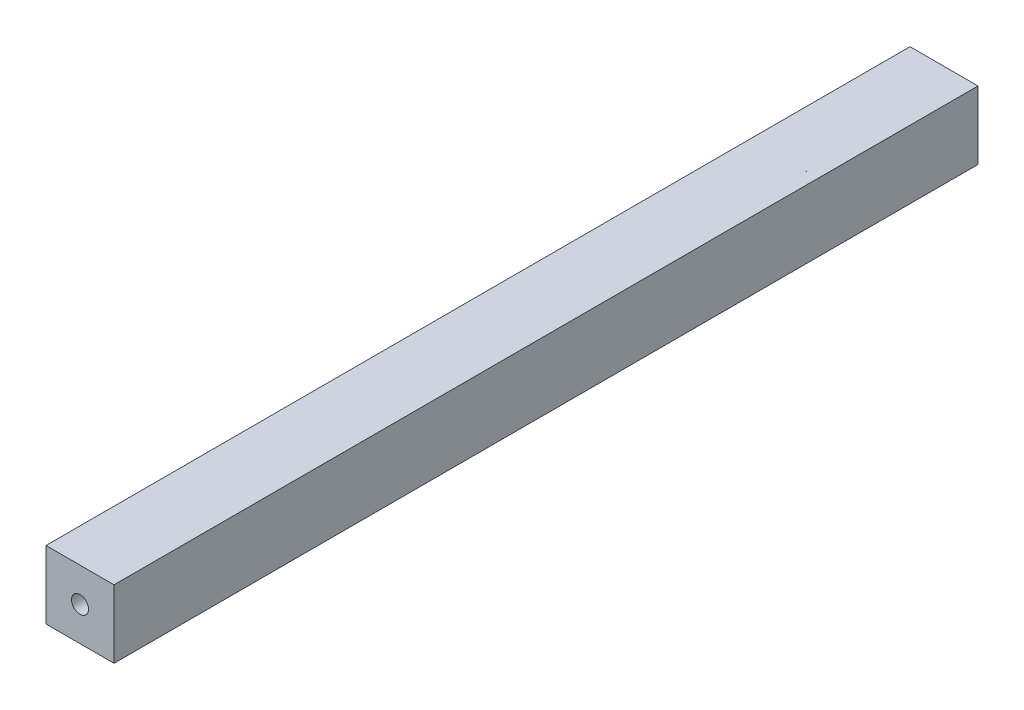
SolidWorks part; units mm, degrees
ref_plane "Front" through (0, 0, 0) normal (0, 0, 1) x (1, 0, 0)
ref_plane "Top" through (0, 0, 0) normal (0, 1, 0) x (1, 0, 0)
ref_plane "Right" through (0, 0, 0) normal (1, 0, 0) x (0, 0, -1)
sketch "Sketch1" plane through (0, 0, 0) normal (0, 0, 1) x (1, 0, 0)
  line L1 (10, 10) -> (-10, 10)
  line L2 (10, 10) -> (10, -10)
  line L3 (10, -10) -> (-10, -10)
  line L4 (-10, 10) -> (-10, -10)
  line L5 (10, 10) -> (-10, -10) construction
  line L6 (10, -10) -> (-10, 10) construction
  point P1 (0, 0)
  dimension "D1" = 20
extrude "Boss-Extrude1" add sketch "Sketch1" along normal blind 254
sketch "Sketch2" plane through (0, 0, 254) normal (0, 0, 1) x (1, 0, 0)
  circle A0 centre (0, 0) radius 2.5
  dimension "D1" = 5
extrude "Cut-Extrude1" cut sketch "Sketch2" against normal up to surface (254 mm away) up to face at (0, 0, 0)
